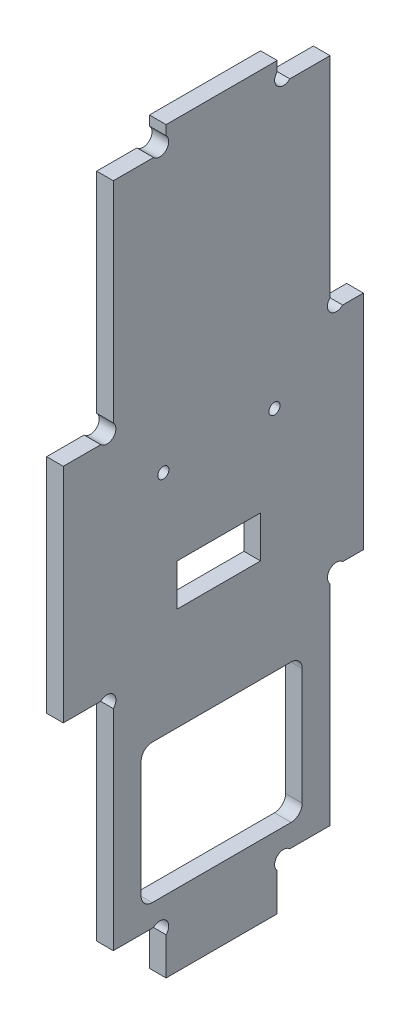
SolidWorks part; units mm, degrees
ref_plane "Plan de face" through (0, 0, 0) normal (0, 0, 1) x (1, 0, 0)
ref_plane "Plan de dessus" through (0, 0, 0) normal (0, 1, 0) x (1, 0, 0)
ref_plane "Plan de droite" through (0, 0, 0) normal (1, 0, 0) x (0, 0, -1)
sketch "Esquisse1" plane through (0, 0, 0) normal (1, 0, 0) x (0, 0, -1)
  line L13 (18.5, 6.7373) -> (18.5, 0)
  line L15 (16.2373, 9) -> (9, 9)
  line L17 (50.2627, 49) -> (54, 49)
  line L18 (6.7373, 49) -> (0, 49)
  line L19 (38.5, 6.7373) -> (38.5, 0)
  line L20 (50.2627, 89) -> (54, 89)
  line L21 (6.7373, 89) -> (0, 89)
  line L22 (18.5, 0) -> (38.5, 0)
  line L23 (40.7627, 9) -> (48, 9)
  line L24 (48, 9) -> (48, 46.7373)
  line L25 (9, 9) -> (9, 46.7373)
  line L26 (54, 89) -> (54, 49)
  line L27 (0, 49) -> (0, 89)
  line L29 (18.5, 131.2627) -> (18.5, 133)
  line L30 (38.5, 131.2627) -> (38.5, 133)
  line L31 (9, 91.2627) -> (9, 129)
  line L32 (9, 129) -> (16.2373, 129)
  line L33 (18.5, 133) -> (38.5, 133)
  line L34 (40.7627, 129) -> (48, 129)
  line L35 (48, 129) -> (48, 91.2627)
  arc A0 (50.2627, 49) -> (48, 46.7373) centre (49.1314, 47.8686) ccw
  arc A1 (9, 46.7373) -> (6.7373, 49) centre (7.8686, 47.8686) ccw
  arc A2 (18.5, 6.7373) -> (16.2373, 9) centre (17.3686, 7.8686) ccw
  arc A3 (38.5, 6.7373) -> (40.7627, 9) centre (39.6314, 7.8686) cw
  arc A4 (9, 91.2627) -> (6.7373, 89) centre (7.8686, 90.1314) cw
  arc A5 (50.2627, 89) -> (48, 91.2627) centre (49.1314, 90.1314) cw
  arc A6 (16.2373, 129) -> (18.5, 131.2627) centre (17.3686, 130.1314) ccw
  arc A7 (40.7627, 129) -> (38.5, 131.2627) centre (39.6314, 130.1314) cw
  point P1 (12.6186, 9)
  dimension "D14" = 1.1314
  dimension "D15" = 1.1314
  dimension "D17" = 1.1314
  dimension "D23" = 1.1314
  dimension "D10" = 1.6
  dimension "D1" = 6
  dimension "D2" = 9
  dimension "D3" = 9.5
  dimension "D4" = 9.5
  dimension "D5" = 9
  dimension "D6" = 40
  dimension "D7" = 40
  dimension "D8" = 40
  dimension "D9" = 4
  dimension "D11" = 1.1314
  dimension "D12" = 1.1314
  dimension "D13" = 1.1314
  dimension "D16" = 20
  dimension "D18" = 1.1314
  dimension "D19" = 1.1314
  dimension "D20" = 1.1314
  dimension "D21" = 1.1314
  dimension "D22" = 1.1314
  dimension "D24" = 3.7373
  dimension "D25" = 1.7373
  dimension "D26" = 1.1314
  dimension "D27" = 7.2373
  dimension "D28" = 1.1314
  dimension "D29" = 1.7373
  dimension "D30" = 20
  dimension "D31" = 39
  dimension "D32" = 39
extrude "Extrusion1" add sketch "Esquisse1" along normal blind 3
sketch "Esquisse2" plane through (0, 0, 0) normal (-1, 0, 0) x (0, 0, 1)
  line L0 (-48, 9) -> (-48, 46.7373) construction
  line L1 (-9, 9) -> (-16.2373, 9) construction
  line L2 (-9, 46.7373) -> (-9, 9) construction
  line L3 (-40.7627, 9) -> (-48, 9) construction
  line L4 (-14, 38) -> (-43, 38)
  line L5 (-14, 38) -> (-14, 13)
  line L6 (-14, 13) -> (-43, 13)
  line L7 (-43, 38) -> (-43, 13)
  line L8 (-48, 9) -> (-48, 46.7373) construction
  line L9 (-9, 46.7373) -> (-9, 9) construction
  circle A0 centre (-38, 79) radius 1
  circle A1 centre (-18, 79) radius 1
  dimension "D1" = 2
  dimension "D2" = 10
  dimension "D3" = 20
  dimension "D4" = 9
  dimension "D5" = 70
  dimension "D6" = 4
  dimension "D7" = 5
  dimension "D8" = 5
  dimension "D9" = 25
extrude "Enlèv. mat.-Extru.1" cut sketch "Esquisse2" against normal through all
fillet "Congé1" radius 2 4 edges at (1.5, 13, -43) (1.5, 13, -14) (1.5, 38, -14) (1.5, 38, -43)
sketch "Esquisse3" plane through (0, 0, 0) normal (-1, 0, 0) x (0, 0, 1)
  line L1 (-35.5, 64) -> (-20.5, 64)
  line L2 (-35.5, 64) -> (-35.5, 56.5)
  line L3 (-35.5, 56.5) -> (-20.5, 56.5)
  line L4 (-20.5, 64) -> (-20.5, 56.5)
  circle A0 centre (-38, 79) radius 1 construction
  circle A1 centre (-18, 79) radius 1 construction
  dimension "D1" = 15
  dimension "D2" = 7.5
  dimension "D3" = 2.5
  dimension "D4" = 2.5
  dimension "D5" = 15
extrude "Enlèv. mat.-Extru.2" cut sketch "Esquisse3" against normal through all
